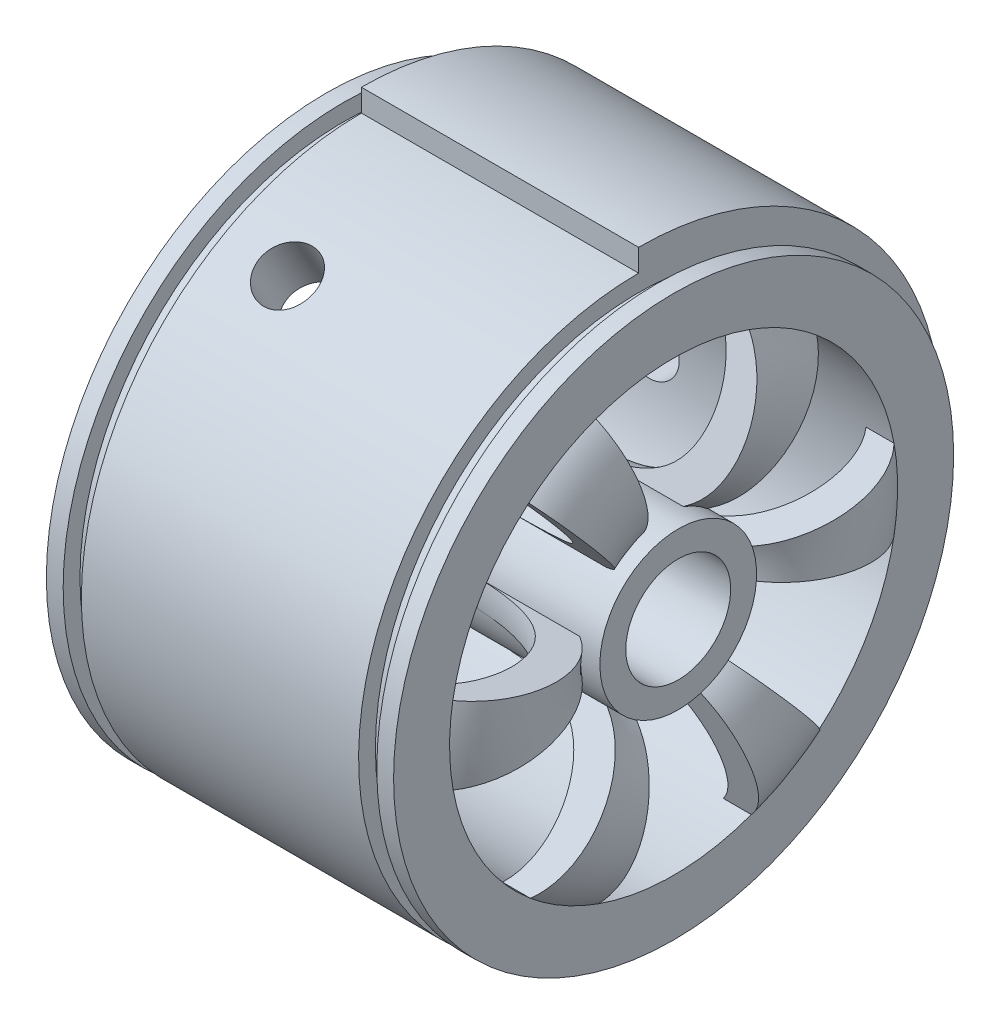
SolidWorks part; units mm, degrees
ref_plane "Front Plane" through (0, 0, 0) normal (0, 0, 1) x (1, 0, 0)
ref_plane "Top Plane" through (0, 0, 0) normal (0, 1, 0) x (1, 0, 0)
ref_plane "Right Plane" through (0, 0, 0) normal (1, 0, 0) x (0, 0, -1)
sketch "Sketch1" plane through (0, 0, 0) normal (0, 0, 1) x (1, 0, 0)
  line L0 (0, 0) -> (49.179, 0) construction
  line L1 (-13, 73.1562) -> (-13, -58.4226) construction
  line L2 (28, 50) -> (28, 47)
  line L3 (-31, 50) -> (-28, 50)
  line L4 (-31, 50) -> (-31, 40)
  line L5 (-31, 40) -> (26, 40)
  line L6 (31, 50) -> (31, 40)
  line L7 (28, 47) -> (24.75, 47)
  line L8 (24.75, 47) -> (24.75, 50)
  line L9 (28, 50) -> (31, 50)
  line L10 (-28, 50) -> (-28, 47)
  line L11 (-28, 47) -> (-24.75, 47)
  line L12 (-24.75, 47) -> (-24.75, 50)
  line L13 (-24.75, 50) -> (24.75, 50)
  line L15 (9.8249, 13.995) -> (9.8249, 9.3629)
  spline S0 degree 3 poles (31, 40) (36.8463, 33.8068) (36.0136, 16.0522) (20.4805, 10.2545) (12.4993, 9.5146) (9.8249, 9.3629) knots 0 0 0 0 0.436989 0.685709 0.818804 0.818804 0.818804 0.818804
  spline S1 degree 3 poles (26, 40) (30.7736, 34.2439) (29.4584, 17.5157) (16.1659, 14.3384) (10.5858, 14.0242) (9.8249, 13.995) knots 0 0 0 0 0.466678 0.747183 0.791718 0.791718 0.791718 0.791718
  dimension "D3" = 13
  dimension "D1" = 62
  dimension "D2" = 10
  dimension "D4" = 50
  dimension "D5" = 3
  dimension "D6" = 3
  dimension "D7" = 3.25
  dimension "D8" = 3
  dimension "D9" = 3
  dimension "D10" = 3.25
  dimension "D13" = 5
revolve "Revolve1" add sketch "Sketch1" angle 360 about L0
sketch "Sketch2" plane through (9.8249, 0, 0) normal (-1, 0, 0) x (0, 0, 1)
  circle A0 centre (0, 0) radius 13.995
  circle A1 centre (0, 0) radius 9.3629
extrude "Boss-Extrude1" add sketch "Sketch2" against normal blind 22
sketch "Sketch4" plane through (-31, 0, 0) normal (-1, 0, 0) x (0, 0, 1)
  line L0 (-4.7229, 13.174) -> (-13.4988, 37.6535)
  line L1 (4.8501, 13.1277) -> (13.8625, 37.5211)
  arc A0 (13.8625, 37.5211) -> (-13.4988, 37.6535) centre (0, 0) ccw
  arc A1 (4.8501, 13.1277) -> (-4.7229, 13.174) centre (0, 0) ccw
  dimension "D1" = 40
extrude "Cut-Extrude1" cut sketch "Sketch4" against normal up to surface (59.0292 mm away) up to face at (28.0292, 0, 13.995)
pattern_circular "CirPattern1" count 6 over 360 about axis through (0, 0, 0) along (1, 0, 0) of "Cut-Extrude1"
sketch "Sketch5" plane through (0, 0, 0) normal (0, 0, 1) x (1, 0, 0)
  line L0 (26, 0) -> (-31, 0) construction
  circle A0 centre (-13, 0) radius 5
  dimension "D1" = 10
  dimension "D2" = 0
  dimension "D3" = 13
extrude "Cut-Extrude2" cut sketch "Sketch5" against normal through all
pattern_circular "CirPattern2" count 3 over 360 of "Cut-Extrude2"
sketch "Sketch6" plane through (0, 0, 0) normal (0, 0, 1) x (1, 0, 0)
  line L1 (-24.75, 50) -> (24.75, 50)
  line L2 (-24.75, 50) -> (-24.75, 54)
  line L3 (-24.75, 54) -> (24.75, 54)
  line L4 (24.75, 50) -> (24.75, 54)
  dimension "D1" = 24.75
  dimension "D2" = 4
revolve "Revolve2" add sketch "Sketch6" angle 80 about axis through (0, 0, 0) along (-1, 0, 0)
sketch "Sketch8" plane through (9.8249, 0, 0) normal (-1, 0, 0) x (0, 0, 1)
  circle A0 centre (0, 0) radius 9.3629 construction
  circle A1 centre (0, 0) radius 9.3629
  arc A12 (4.8501, 13.1277) -> (-4.7229, 13.174) centre (0, 0) ccw
  arc A13 (-4.7229, 13.174) -> (-8.9438, 10.7642) centre (0, 0) ccw
  arc A14 (-8.9438, 10.7642) -> (-13.7705, 2.4969) centre (0, 0) ccw
  arc A15 (-13.7705, 2.4969) -> (-13.794, -2.3635) centre (0, 0) ccw
  arc A16 (-13.794, -2.3635) -> (-9.0476, -10.6771) centre (0, 0) ccw
  arc A17 (-9.0476, -10.6771) -> (-4.8501, -13.1277) centre (0, 0) ccw
  arc A18 (-4.8501, -13.1277) -> (4.7229, -13.174) centre (0, 0) ccw
  arc A19 (4.7229, -13.174) -> (8.9438, -10.7642) centre (0, 0) ccw
  arc A20 (8.9438, -10.7642) -> (13.7705, -2.4969) centre (0, 0) ccw
  arc A21 (13.7705, -2.4969) -> (13.794, 2.3635) centre (0, 0) ccw
  arc A22 (13.794, 2.3635) -> (9.0476, 10.6771) centre (0, 0) ccw
  arc A23 (9.0476, 10.6771) -> (4.8501, 13.1277) centre (0, 0) ccw
  arc A24 (4.8501, 13.1277) -> (-4.7229, 13.174) centre (0, 0) ccw
  arc A25 (-4.7229, 13.174) -> (-8.9438, 10.7642) centre (0, 0) ccw
  arc A26 (-8.9438, 10.7642) -> (-13.7705, 2.4969) centre (0, 0) ccw
  arc A27 (-13.7705, 2.4969) -> (-13.794, -2.3635) centre (0, 0) ccw
  arc A28 (-13.794, -2.3635) -> (-9.0476, -10.6771) centre (0, 0) ccw
  arc A29 (-9.0476, -10.6771) -> (-4.8501, -13.1277) centre (0, 0) ccw
  arc A30 (-4.8501, -13.1277) -> (4.7229, -13.174) centre (0, 0) ccw
  arc A31 (4.7229, -13.174) -> (8.9438, -10.7642) centre (0, 0) ccw
  arc A32 (8.9438, -10.7642) -> (13.7705, -2.4969) centre (0, 0) ccw
  arc A33 (13.7705, -2.4969) -> (13.794, 2.3635) centre (0, 0) ccw
  arc A34 (13.794, 2.3635) -> (9.0476, 10.6771) centre (0, 0) ccw
  arc A35 (9.0476, 10.6771) -> (4.8501, 13.1277) centre (0, 0) ccw
  dimension "D1" = 0
extrude "Boss-Extrude2" add sketch "Sketch8" along normal blind 10
